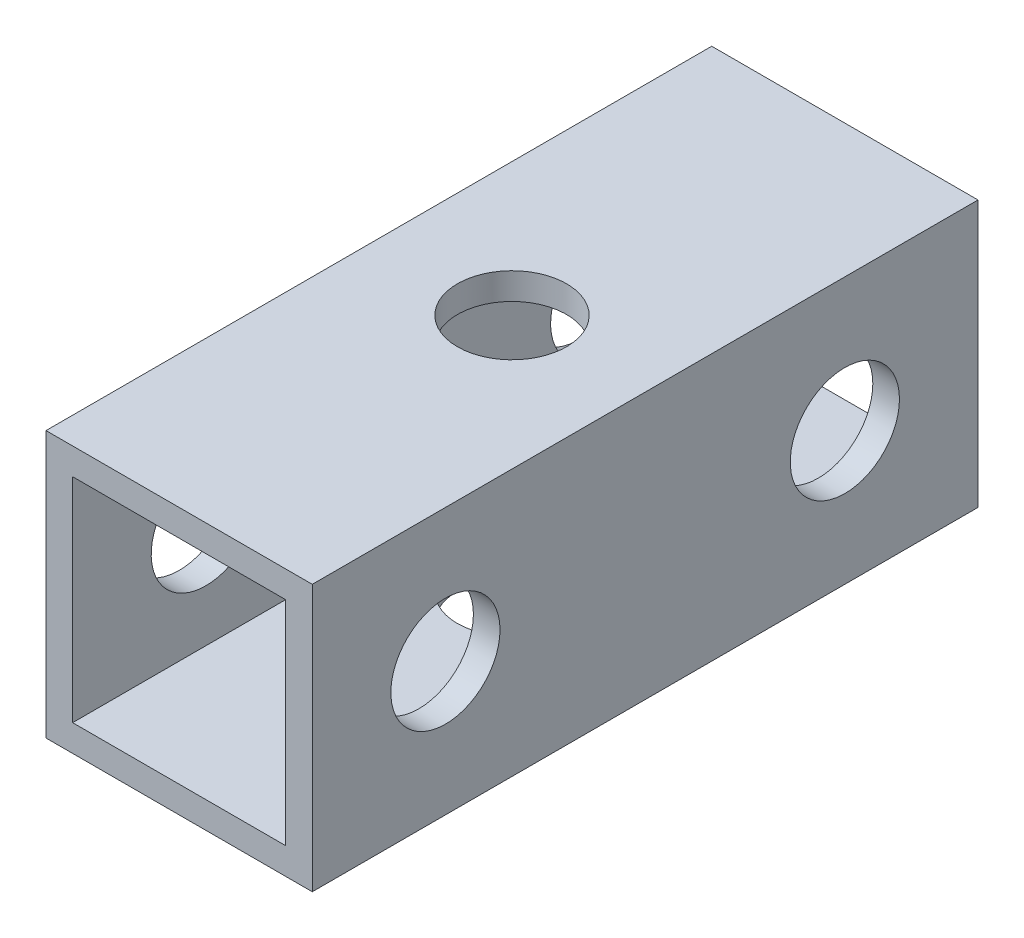
SolidWorks part; units mm, degrees
ref_plane "前视基准面" through (0, 0, 0) normal (0, 0, 1) x (1, 0, 0)
ref_plane "上视基准面" through (0, 0, 0) normal (0, 1, 0) x (1, 0, 0)
ref_plane "右视基准面" through (0, 0, 0) normal (1, 0, 0) x (0, 0, -1)
sketch "草图1" plane through (0, 0, 0) normal (0, 0, 1) x (1, 0, 0)
  line L0 (5, -5) -> (5, 5)
  line L1 (4, -4) -> (-4, -4)
  line L2 (4, -4) -> (4, 4)
  line L3 (4, 4) -> (-4, 4)
  line L4 (-4, -4) -> (-4, 4)
  line L5 (4, -4) -> (-4, 4) construction
  line L6 (4, 4) -> (-4, -4) construction
  line L7 (5, 5) -> (-5, 5)
  line L8 (-5, -5) -> (-5, 5)
  line L9 (5, -5) -> (-5, -5)
  point P0 (0, 0)
  dimension "D1" = 1
  dimension "D2" = 10
extrude "凸台-拉伸1" add sketch "草图1" along normal mid plane 25
sketch "草图2" plane through (0, 5, 0) normal (0, 1, 0) x (1, 0, 0)
  circle A0 centre (0, 0) radius 2.05
  dimension "D1" = 4.1
extrude "切除-拉伸1" cut sketch "草图2" against normal through all
sketch "草图3" plane through (5, 0, 0) normal (1, 0, 0) x (0, 0, -1)
  line L0 (7.5, 0) -> (-7.5, 0) construction
  circle A0 centre (-7.5, 0) radius 2.05
  circle A1 centre (7.5, 0) radius 2.05
  point P4 (0, 0)
  dimension "D2" = 4.1
  dimension "D1" = 15
extrude "切除-拉伸2" cut sketch "草图3" against normal through all
